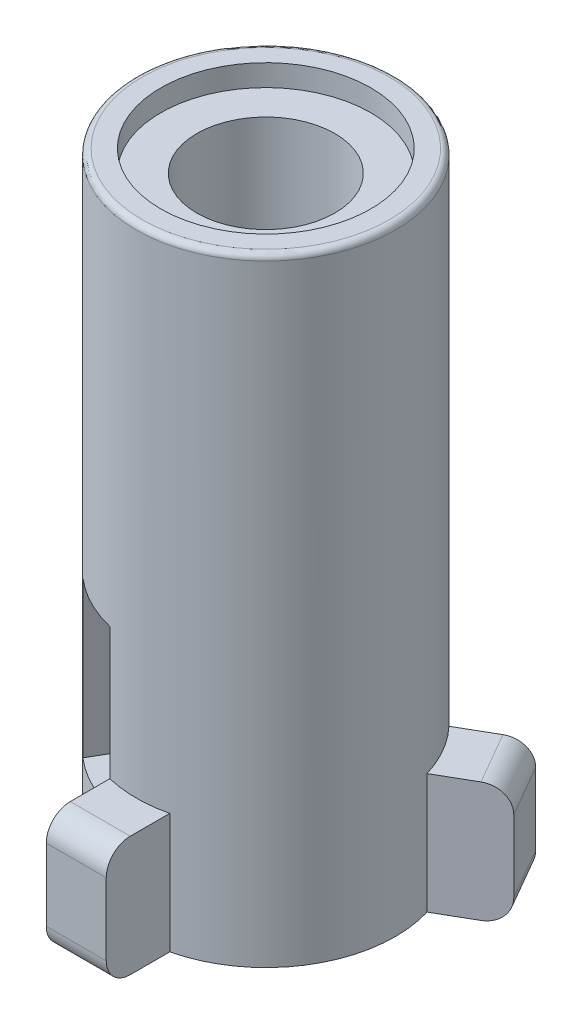
SolidWorks part; units mm, degrees
ref_plane "Front Plane" through (0, 0, 0) normal (0, 0, 1) x (1, 0, 0)
ref_plane "Top Plane" through (0, 0, 0) normal (0, 1, 0) x (1, 0, 0)
ref_plane "Right Plane" through (0, 0, 0) normal (1, 0, 0) x (0, 0, -1)
sketch "Sketch1" plane through (0, 0, 0) normal (0, 1, 0) x (1, 0, 0)
  circle A0 centre (0, 0) radius 5.4
extrude "Boss-Extrude1" add sketch "Sketch1" along normal blind 25.75
sketch "Sketch2" plane through (0, 0, 0) normal (0, -1, 0) x (1, 0, 0)
  line L0 (0, 0) -> (0, 5.7512) construction
  line L1 (0, 0) -> (-6.2914, -3.6323) construction
  line L2 (0, 0) -> (7.4175, -4.2825) construction
  line L3 (2.7381, -0.1375) -> (7.4666, -2.8675)
  line L4 (-1.25, 7.9) -> (1.25, 7.9)
  line L5 (-1.25, 7.9) -> (-1.25, 2.4368)
  line L6 (-1.25, 2.4368) -> (1.25, 2.4368)
  line L7 (1.25, 7.9) -> (1.25, 2.4368)
  line L8 (7.4666, -2.8675) -> (6.2166, -5.0325)
  line L9 (6.2166, -5.0325) -> (1.4881, -2.3025)
  line L10 (1.4881, -2.3025) -> (2.7381, -0.1375)
  line L11 (-2.7381, -0.1375) -> (-1.4881, -2.3025)
  line L12 (-1.4881, -2.3025) -> (-6.2166, -5.0325)
  line L13 (-6.2166, -5.0325) -> (-7.4666, -2.8675)
  line L14 (-7.4666, -2.8675) -> (-2.7381, -0.1375)
  dimension "D1" = 1.25
  dimension "D2" = 1.25
  dimension "D3" = 7.9
  dimension "D4" = 1.25
  dimension "D5" = 1.25
  dimension "D6" = 5.46
  dimension "D7" = 7.9
  dimension "D8" = 5.46
  dimension "D9" = 1.25
  dimension "D10" = 1.25
  dimension "D11" = 7.9
extrude "Boss-Extrude2" add sketch "Sketch2" against normal blind 5
fillet "Fillet1" radius 1 6 edges at (-6.8416, 0, -3.95) (-6.8416, 5, -3.95) (0, 0, 7.9) (0, 5, 7.9) (6.8416, 0, -3.95) (6.8416, 5, -3.95)
fillet "Fillet2" radius 0.25 1 edges at (0, 25.75, 5.4)
sketch "Sketch4" plane through (0, 0, 0) normal (0, -1, 0) x (1, 0, 0)
  circle A0 centre (0, 0) radius 2.875
extrude "Cut-Extrude1" cut sketch "Sketch4" against normal blind 25.75 contours A0
sketch "Sketch5" plane through (0, 0, 0) normal (0, -1, 0) x (-1, 0, 0)
  circle A0 centre (0, 0) radius 4.375
extrude "Cut-Extrude2" cut sketch "Sketch5" against normal blind 0.9
sketch "Sketch6" plane through (0, 25.75, 0) normal (0, 1, 0) x (1, 0, 0)
  circle A0 centre (0, 0) radius 4.375
extrude "Cut-Extrude3" cut sketch "Sketch6" against normal blind 0.9
sketch "Sketch7" plane through (0, 0, 0) normal (0, -1, 0) x (1, 0, 0)
  line L0 (0, 0) -> (-5.9756, -3.45) construction
  line L1 (-6.6006, -2.3675) -> (-5.3506, -4.5325) construction
  line L2 (-5.9756, -3.45) -> (4.6765, 2.7) construction
  arc A0 (5.1745, -1.5441) -> (1.25, 5.2533) centre (0, 0) ccw construction
ref_plane "Plane1" through (0, 0, 0) normal (-0.5, 0, 0.866) x (0.866, 0, 0.5)
sketch "Sketch8" plane through (0, 0, 0) normal (0, -1, 0) x (1, 0, 0)
  line L0 (-1.25, 5.2533) -> (3.9245, -3.7092) construction
  line L1 (3.9245, -3.7092) -> (6.8399, -8.7587) construction
sketch "Sketch9" plane through (0, 0, 0) normal (-0.5, 0, 0.866) x (0.866, 0, 0.5)
  line L0 (1.5441, 0) -> (1.5441, 5) construction
  line L1 (1.5441, 4) -> (-1.0559, 4)
  line L2 (1.5441, 4) -> (1.5441, 10.5)
  line L3 (1.5441, 10.5) -> (-1.0559, 10.5)
  line L4 (-1.0559, 4) -> (-1.0559, 10.5)
  line L8 (-5.2533, 0) -> (1.5441, 0) construction
  dimension "D1" = 2.6
  dimension "D2" = 6.5
  dimension "D3" = 10.5
extrude "Cut-Extrude4" cut sketch "Sketch9" along normal blind 10
